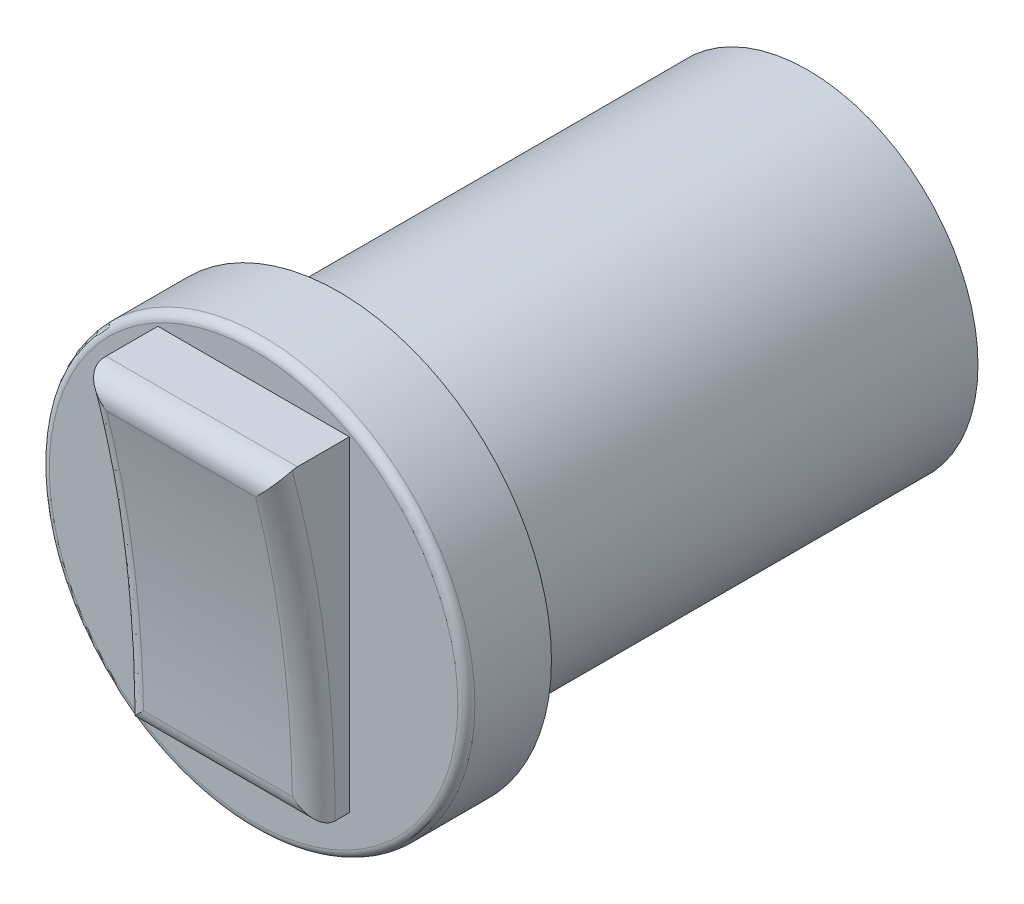
SolidWorks part; units mm, degrees
ref_plane "Front Plane" through (0, 0, 0) normal (0, 0, 1) x (1, 0, 0)
ref_plane "Top Plane" through (0, 0, 0) normal (0, 1, 0) x (1, 0, 0)
ref_plane "Right Plane" through (0, 0, 0) normal (1, 0, 0) x (0, 0, -1)
sketch "Sketch1" plane through (0, 0, 0) normal (0, 0, 1) x (1, 0, 0)
  circle A0 centre (0, 0) radius 10.16
  dimension "D1" = 20.32
extrude "Boss-Extrude1" add sketch "Sketch1" along normal blind 28
sketch "Sketch2" plane through (0, 0, 28) normal (0, 0, 1) x (1, 0, 0)
  circle A0 centre (0, 0) radius 12.7
  dimension "D1" = 25.4
extrude "Boss-Extrude2" add sketch "Sketch2" along normal blind 5.08
sketch "Sketch3" plane through (0, 0, 0) normal (1, 0, 0) x (0, 0, -1)
  line L0 (-33.08, -8.8337) -> (-33.08, 10.5941)
  line L1 (-33.08, 12.7) -> (-33.08, -12.7) construction
  line L2 (-33.08, 10.5941) -> (-37.8241, 10.5941)
  line L3 (-35.1996, -8.8337) -> (-33.08, -8.8337)
  spline S0 degree 2 poles (-37.8241, 10.5941) (-35.1987, 1.0748) (-35.1996, -8.8337) knots 0 0 0 1 1 1
extrude "Boss-Extrude3" add sketch "Sketch3" along normal mid plane 11.43
fillet "Fillet1" radius 1.27 4 edges at (0, 10.5941, 37.8241) (0, -8.8337, 35.1996)
fillet "Fillet2" radius 0.508 1 edges at (12.7, 0, 33.08)
